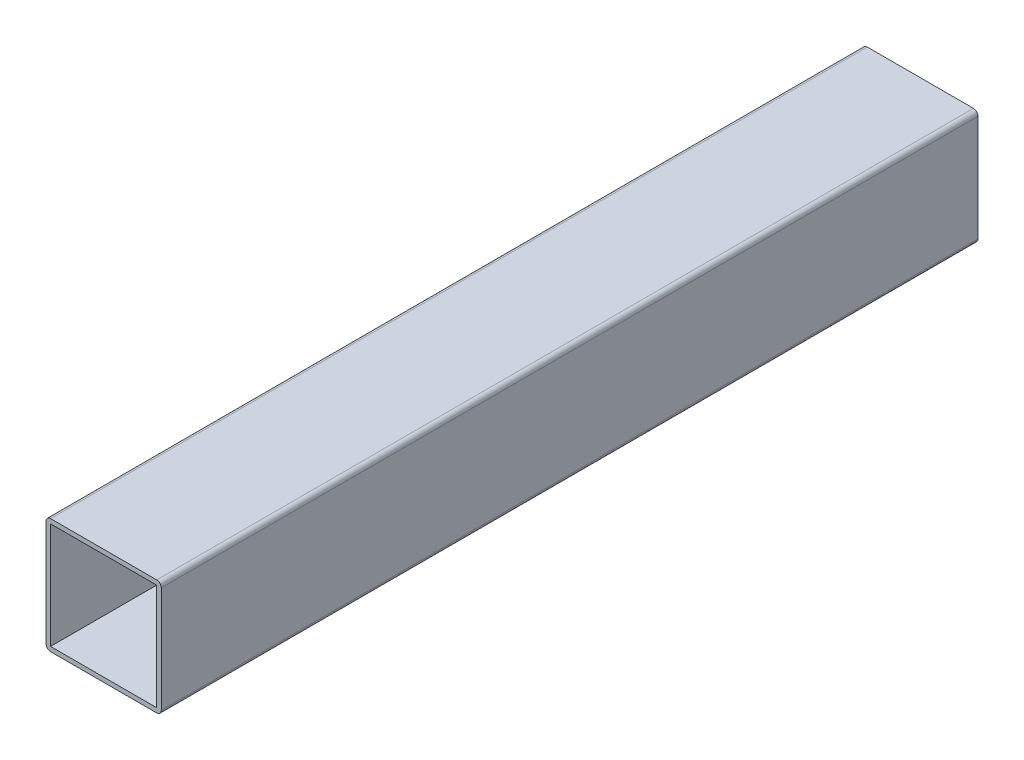
SolidWorks part; units mm, degrees
material "Plain Carbon Steel"
ref_plane "Alzado" through (0, 0, 0) normal (0, 0, 1) x (1, 0, 0)
ref_plane "Planta" through (0, 0, 0) normal (0, 1, 0) x (1, 0, 0)
ref_plane "Vista lateral" through (0, 0, 0) normal (1, 0, 0) x (0, 0, -1)
sketch "Croquis1" plane through (0, 0, 0) normal (0, 0, 1) x (1, 0, 0)
  line L0 (-11.7, 11.7) -> (11.7, 11.7)
  line L1 (-11.7, -12.7) -> (11.7, -12.7)
  line L2 (-12.7, -11.7) -> (-12.7, 11.7)
  line L3 (-11.7, 12.7) -> (11.7, 12.7)
  line L4 (12.7, -11.7) -> (12.7, 11.7)
  line L5 (-12.7, -12.7) -> (12.7, 12.7) construction
  line L6 (-12.7, 12.7) -> (12.7, -12.7) construction
  line L7 (11.7, -11.7) -> (11.7, 11.7)
  line L8 (-11.7, -11.7) -> (11.7, -11.7)
  line L9 (-11.7, -11.7) -> (-11.7, 11.7)
  arc A0 (-11.7, -12.7) -> (-12.7, -11.7) centre (-11.7, -11.7) cw
  arc A1 (11.7, -12.7) -> (12.7, -11.7) centre (11.7, -11.7) ccw
  arc A2 (11.7, 12.7) -> (12.7, 11.7) centre (11.7, 11.7) cw
  arc A3 (-12.7, 11.7) -> (-11.7, 12.7) centre (-11.7, 11.7) cw
  arc A4 (11.7, 11.7) -> (11.7, 11.7) centre (11.7, 11.7) cw
  arc A5 (11.7, -11.7) -> (11.7, -11.7) centre (11.7, -11.7) ccw
  arc A6 (-11.7, -11.7) -> (-11.7, -11.7) centre (-11.7, -11.7) cw
  arc A7 (-11.7, 11.7) -> (-11.7, 11.7) centre (-11.7, 11.7) cw
  point P0 (0, 0)
  dimension "D2" = 1
  dimension "D1" = 25.4
  dimension "D3" = 1
extrude "Saliente-Extruir1" add sketch "Croquis1" against normal blind 180
ref_plane "Bearing Housing Midplane" through (0.3898, 50.6048, -13.9987) normal (-0.0074, -0.9638, 0.2666) x (-1, 0.0071, -0.0021)
ref_plane "Front Roll Hoop Plane" through (0, 0, 0) normal (0.0074, 0.9638, -0.2666) x (1, -0.0072, 0.0019)
